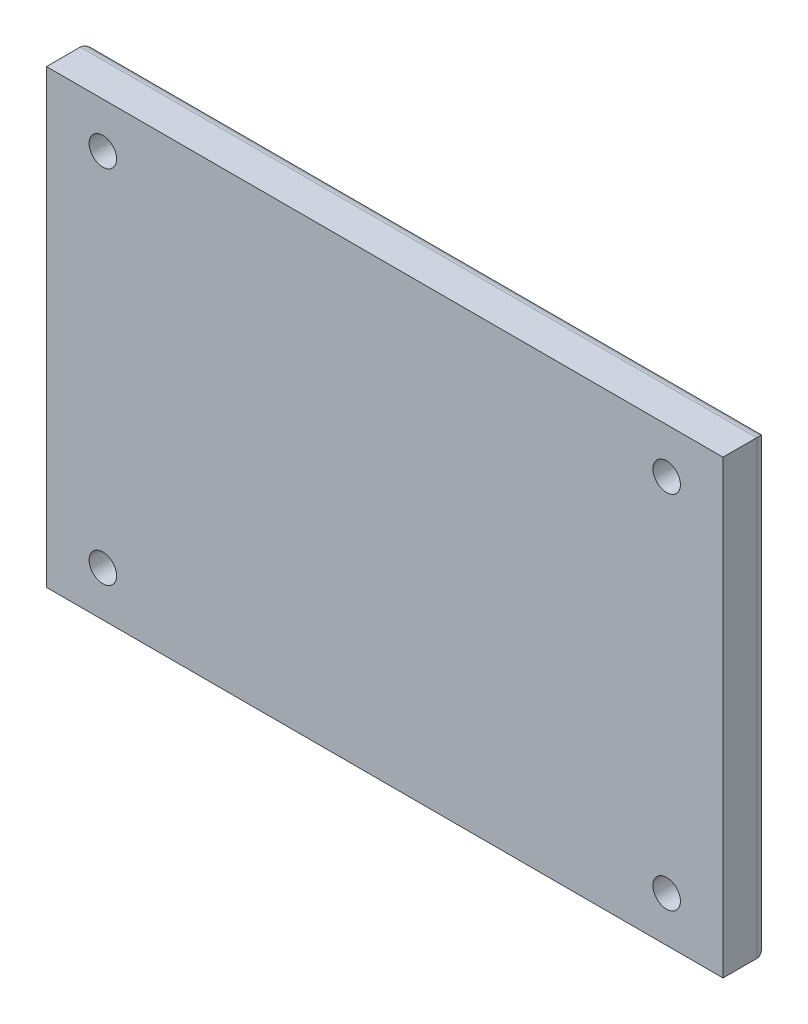
SolidWorks part; units mm, degrees
ref_plane "Front Plane" through (0, 0, 0) normal (0, 0, 1) x (1, 0, 0)
ref_plane "Top Plane" through (0, 0, 0) normal (0, 1, 0) x (1, 0, 0)
ref_plane "Right Plane" through (0, 0, 0) normal (1, 0, 0) x (0, 0, -1)
sketch "Sketch1" plane through (0, 0, 0) normal (0, 0, 1) x (1, 0, 0)
  line L0 (0, 0) -> (-25, 0) construction
  line L1 (-30, 20) -> (30, 20)
  line L2 (-30, 20) -> (-30, -20)
  line L3 (-30, -20) -> (30, -20)
  line L4 (30, 20) -> (30, -20)
  line L5 (-30, 20) -> (30, -20) construction
  line L6 (-30, -20) -> (30, 20) construction
  line L7 (-25, 0) -> (-25, 16) construction
  line L8 (-25, 0) -> (-25, -16) construction
  line L9 (0, 0) -> (25, 0) construction
  line L10 (25, 0) -> (25, 16) construction
  line L11 (25, 0) -> (25, -16) construction
  point P0 (0, 0)
extrude "Boss-Extrude1" add sketch "Sketch1" along normal blind 4
fillet "Fillet1" radius 1 4 edges at (0, 20, 0) (-30, 0, 0) (0, -20, 0) (30, 0, 0)
sketch "Sketch3" plane through (0, 0, 0) normal (0, 0, -1) x (-1, 0, 0)
  line L0 (29, -19) -> (-29, 19) construction
  line L1 (29, 19) -> (-29, -19) construction
  line L2 (0, 0) -> (-25, 0) construction
  line L3 (-25, 0) -> (-25, -16) construction
  line L4 (-25, 0) -> (-25, 16) construction
  line L5 (0, 0) -> (25, 0) construction
  line L6 (25, 0) -> (25, -16) construction
  line L7 (25, 0) -> (25, 16) construction
hole_wizard "CBORE for #2 Socket Head Cap Screw1" positions "3DSketch1" profile "Sketch4" counterbore size "#2" standard "ANSI Inch"
sketch3d "3DSketch1"
  point P0 (-25, -16, 0)
  point P3 (-25, 16, 0)
  point P6 (25, 16, 0)
  point P9 (25, -16, 0)
sketch "Sketch4" plane through (-25, -16, 0) normal (1, 0, 0) x (0, 1, 0)
  line L0 (0, 0) -> (0, 15.7326)
  line L1 (0, 15.7326) -> (1.2192, 15)
  line L2 (1.2192, 15) -> (1.2192, 2.1844)
  line L3 (1.2192, 2.1844) -> (2.3812, 2.1844)
  line L4 (2.3812, 2.1844) -> (2.3812, 0)
  line L5 (2.3812, 0) -> (0, 0)
  line L10 (0, 15.7326) -> (-1.2192, 15) construction
  line L11 (0, -6.35) -> (0, 107.95) construction
  dimension "Hole Dia." = 2.4384
  dimension "Hole Depth" = 15
  dimension "C'Bore Dia." = 4.7625
  dimension "C'Bore Depth" = 2.1844
  dimension "Drill Angle" = 118
